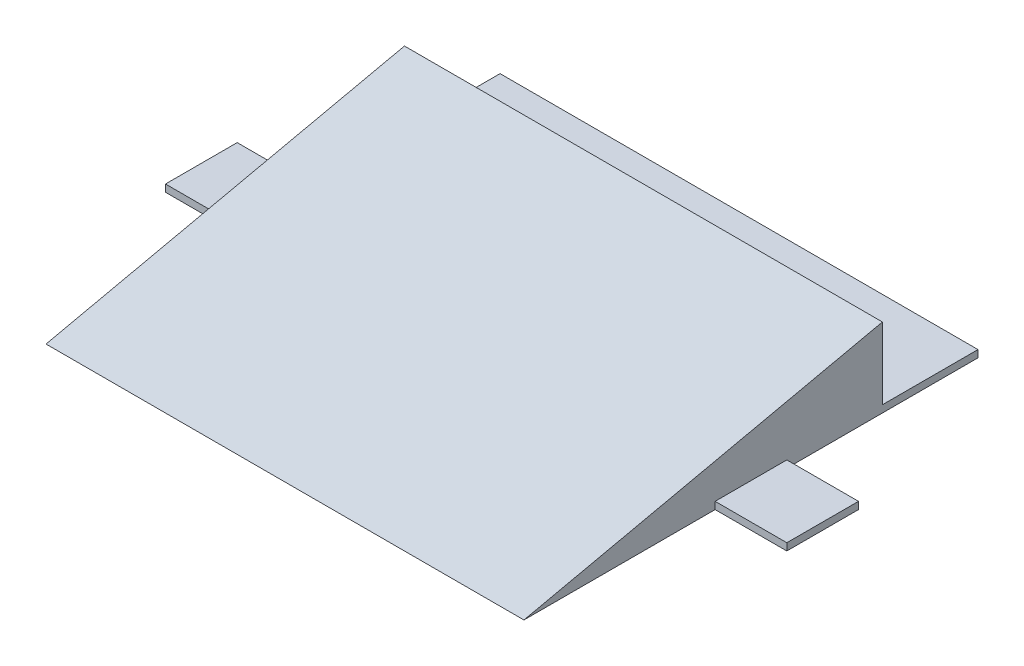
SolidWorks part; units mm, degrees
ref_plane "Front Plane" through (0, 0, 0) normal (0, 0, 1) x (1, 0, 0)
ref_plane "Top Plane" through (0, 0, 0) normal (0, 1, 0) x (1, 0, 0)
ref_plane "Right Plane" through (0, 0, 0) normal (1, 0, 0) x (0, 0, -1)
sketch "Sketch1" plane through (0, 0, 0) normal (1, 0, 0) x (0, 0, -1)
  line L0 (-75, 0) -> (0, 16.5)
  line L1 (0, 16.5) -> (0, 0)
  line L2 (0, 0) -> (-75, 0)
  point P2 (-36.2652, 0)
  dimension "D1" = 16.5
  dimension "D2" = 75
extrude "Boss-Extrude1" add sketch "Sketch1" along normal mid plane 100
sketch "Sketch2" plane through (50, 0, 0) normal (1, 0, 0) x (0, 0, -1)
  line L1 (0, 0) -> (20, 0)
  line L2 (0, 0) -> (0, 1.5)
  line L3 (0, 1.5) -> (20, 1.5)
  line L4 (20, 0) -> (20, 1.5)
  point P5 (19.1771, 2.8267)
  dimension "D1" = 1.5
  dimension "D2" = 20
extrude "Boss-Extrude2" add sketch "Sketch2" against normal up to surface (100 mm away) up to face at (-50, 5.5, 25)
sketch "Sketch3" plane through (0, 0, 0) normal (0, -1, 0) x (1, 0, 0)
  line L0 (50, 75) -> (50, -20) construction
  line L1 (50, 35) -> (65, 35)
  line L2 (50, 35) -> (50, 20)
  line L3 (50, 20) -> (65, 20)
  line L4 (65, 35) -> (65, 20)
  line L5 (50, 75) -> (50, -20) construction
  line L6 (0, -20) -> (0, 75) construction
  line L7 (-50, -20) -> (50, -20) construction
  line L8 (50, 75) -> (-50, 75) construction
  line L9 (-50, 20) -> (-65, 20)
  line L10 (-65, 35) -> (-65, 20)
  line L11 (-50, 35) -> (-65, 35)
  line L12 (-50, 35) -> (-50, 20)
  point P10 (50, 27.5)
  point P11 (50, 27.5)
  dimension "D1" = 15
  dimension "D2" = 15
extrude "Boss-Extrude3" add sketch "Sketch3" against normal up to surface (1.5 mm away) up to face at (0, 1.5, -10)
